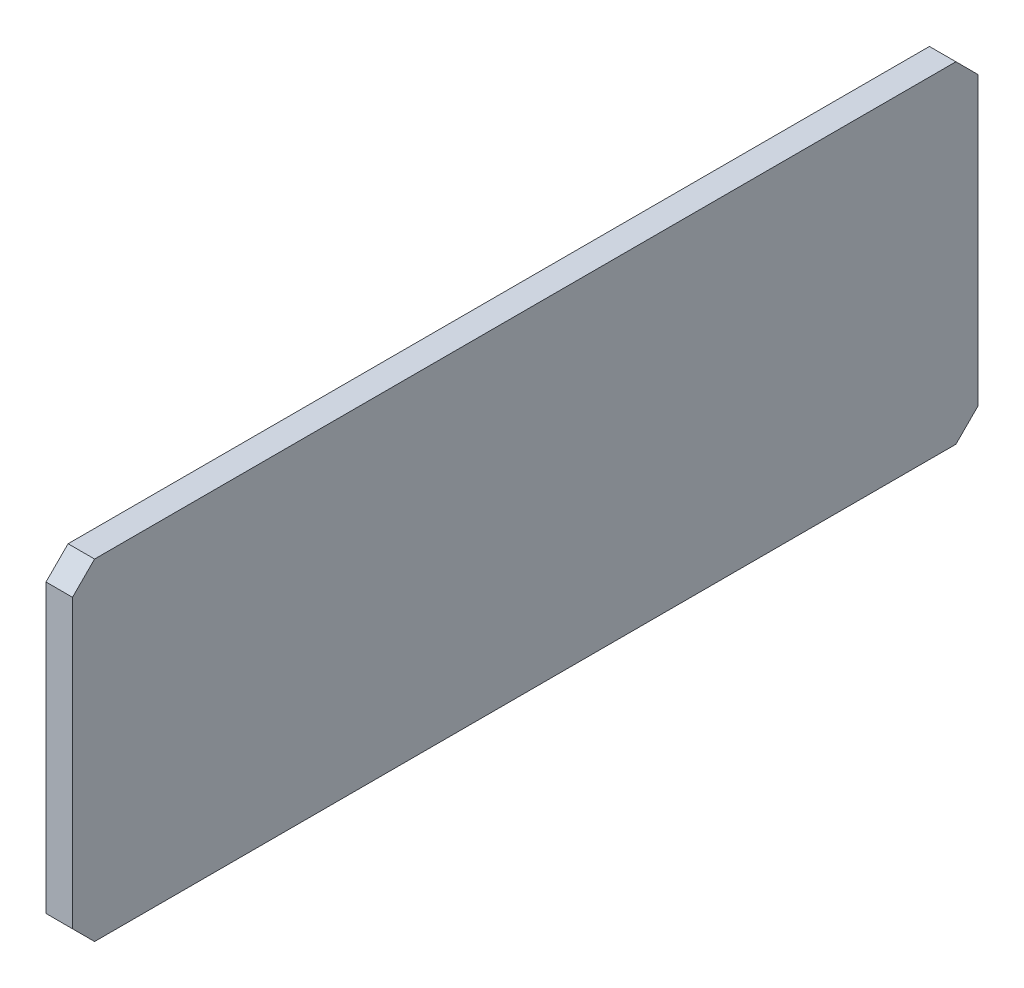
SolidWorks part; units mm, degrees
material "Acier allié"
ref_plane "Plan de face" through (0, 0, 0) normal (0, 0, 1) x (1, 0, 0)
ref_plane "Plan de dessus" through (0, 0, 0) normal (0, 1, 0) x (1, 0, 0)
ref_plane "Plan de droite" through (0, 0, 0) normal (1, 0, 0) x (0, 0, -1)
sketch "Esquisse1" plane through (0, 0, 0) normal (0, 0, 1) x (1, 0, 0)
  line L1 (-6, -75) -> (6, -75)
  line L2 (-6, -75) -> (-6, 75)
  line L3 (-6, 75) -> (6, 75)
  line L4 (6, -75) -> (6, 75)
  line L5 (-6, -75) -> (6, 75) construction
  line L6 (-6, 75) -> (6, -75) construction
  point P0 (0, 0)
  dimension "D1" = 150
  dimension "D2" = 12
extrude "Boss.-Extru.1" add sketch "Esquisse1" along normal blind 410
chamfer "Chanfrein1" distance 10 angle 45 4 edges at (0, 75, 0) (0, -75, 0) (0, -75, 410) (0, 75, 410)
